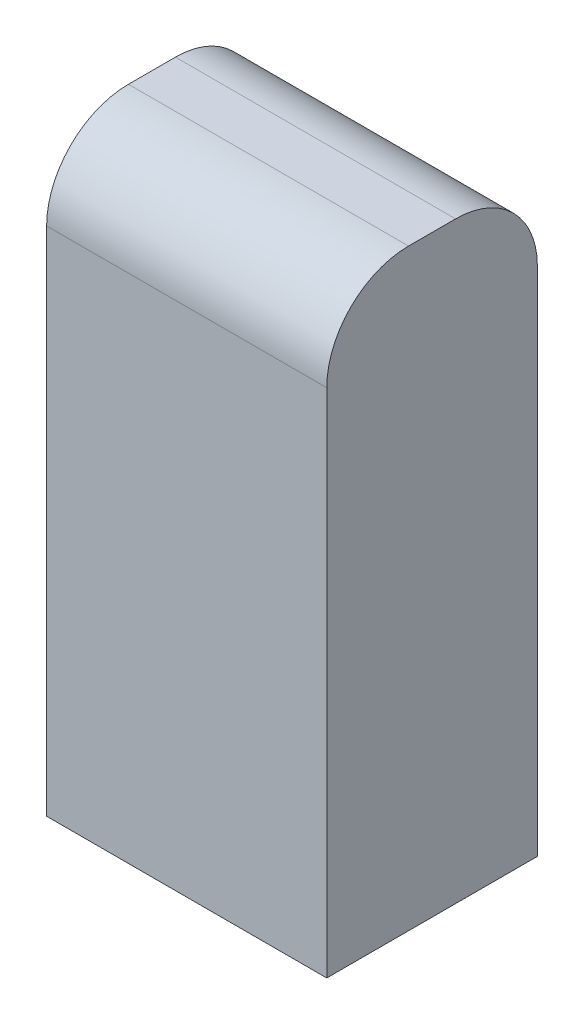
SolidWorks part; units mm, degrees
ref_plane "Front Plane" through (0, 0, 0) normal (0, 0, 1) x (1, 0, 0)
ref_plane "Top Plane" through (0, 0, 0) normal (0, 1, 0) x (1, 0, 0)
ref_plane "Right Plane" through (0, 0, 0) normal (1, 0, 0) x (0, 0, -1)
sketch "Sketch1" plane through (0, 0, 0) normal (0, 1, 0) x (1, 0, 0)
  line L1 (-17.399, -13.081) -> (17.399, -13.081)
  line L2 (-17.399, -13.081) -> (-17.399, 13.081)
  line L3 (-17.399, 13.081) -> (17.399, 13.081)
  line L4 (17.399, -13.081) -> (17.399, 13.081)
  line L5 (-17.399, -13.081) -> (17.399, 13.081) construction
  line L6 (-17.399, 13.081) -> (17.399, -13.081) construction
  point P0 (0, 0)
  dimension "D1" = 34.798
  dimension "D2" = 26.162
extrude "Boss-Extrude1" add sketch "Sketch1" along normal blind 73.66
fillet "Fillet1" radius 10.16 2 edges at (0, 73.66, -13.081) (0, 73.66, 13.081)
